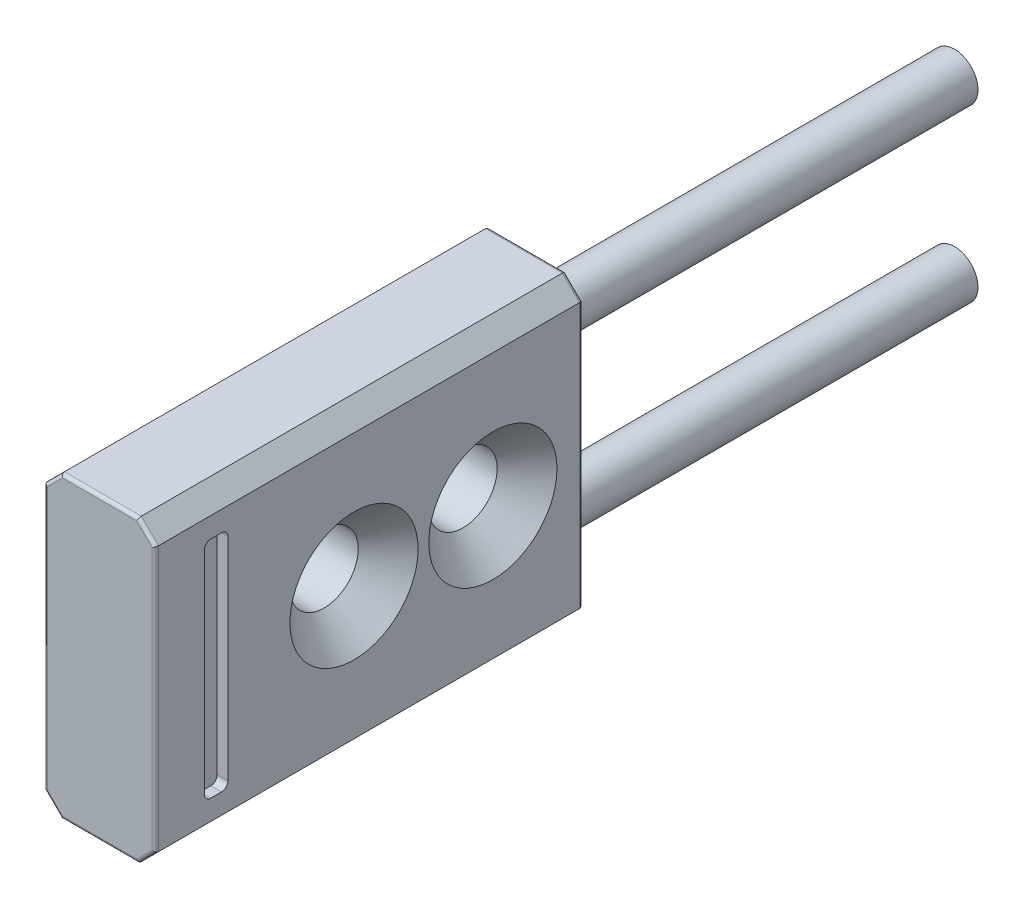
SolidWorks part; units mm, degrees
ref_plane "Front Plane" through (0, 0, 0) normal (0, 0, 1) x (1, 0, 0)
ref_plane "Top Plane" through (0, 0, 0) normal (0, 1, 0) x (1, 0, 0)
ref_plane "Right Plane" through (0, 0, 0) normal (1, 0, 0) x (0, 0, -1)
sketch "Sketch1" plane through (0, 0, 0) normal (1, 0, 0) x (0, 0, -1)
  line L0 (17.1, -7) -> (17.1, 7)
  line L1 (17.1, 7) -> (-2.9, 7)
  line L2 (-2.9, 7) -> (-2.9, -7)
  line L3 (-2.9, -7) -> (17.1, -7)
extrude "Boss-Extrude1" add sketch "Sketch1" against normal blind 5.2
sketch "Sketch2" plane through (0, 0, 0) normal (1, 0, 0) x (0, 0, -1)
  line L0 (0.5, -5.25) -> (0.5, 5.25)
  line L1 (0.5, 5.25) -> (-0.6, 5.25)
  line L2 (-0.6, 5.25) -> (-0.6, -5.25)
  line L3 (-0.6, -5.25) -> (0.5, -5.25)
extrude "Cut-Extrude1" cut sketch "Sketch2" against normal blind 0.5
ref_plane "Plane1" through (0, -4, 0) normal (0, 1, 0) x (1, 0, 0)
sketch "Sketch3" plane through (0, -4, 0) normal (0, 1, 0) x (1, 0, 0)
  line L0 (-1.5, 37.1) -> (-2.6, 37.1)
  line L1 (-2.6, 37.1) -> (-2.6, 17.1)
  line L2 (-2.6, 17.1) -> (-1.5, 17.1)
  line L3 (-1.5, 17.1) -> (-1.5, 37.1)
  line L4 (-2.6, 37.1) -> (-2.6, 17.1) construction
revolve "Revolve1" add sketch "Sketch3" angle 360 about L4
ref_plane "Plane2" through (0, 4, 0) normal (0, 1, 0) x (1, 0, 0)
sketch "Sketch4" plane through (0, 4, 0) normal (0, 1, 0) x (1, 0, 0)
  line L0 (-1.5, 37.1) -> (-2.6, 37.1)
  line L1 (-2.6, 37.1) -> (-2.6, 17.1)
  line L2 (-2.6, 17.1) -> (-1.5, 17.1)
  line L3 (-1.5, 17.1) -> (-1.5, 37.1)
  line L4 (-2.6, 37.1) -> (-2.6, 17.1) construction
revolve "Revolve2" add sketch "Sketch4" angle 360 about L4
hole_wizard "Ø3.2 (3.2) Diameter Hole1" positions "Sketch6" profile "Sketch5" hole size "Ø3.2" standard "ANSI Metric"
sketch "Sketch6" plane through (0, 0, 0) normal (1, 0, 0) x (0, 0, -1)
  point P0 (12.9, 0)
  point P1 (6.4, 0)
sketch "Sketch5" plane through (0, 0, -12.9) normal (0, 1, 0) x (0, 0, -1)
  line L0 (0, 0) -> (0, 5.2)
  line L1 (0, 5.2) -> (1.6, 5.2)
  line L2 (1.6, 5.2) -> (1.6, 0)
  line L5 (1.6, 0) -> (0, 0)
  line L11 (0, -6.35) -> (0, 107.95) construction
  dimension "Thru Hole Dia." = 3.2
  dimension "Thru Hole Depth" = 5.2
chamfer "Chamfer1" distance 0.8 angle 45 4 edges at (0, 7, -7.1) (0, -7, -7.1) (-5.2, -7, -7.1) (-5.2, 7, -7.1)
chamfer "Chamfer2" distance 1.4 angle 45 2 edges at (0, 0, -14.5) (0, 0, -8)
fillet "Fillet1" radius 0.15 16 edges at (-0.4, 6.6, -17.1) (0, 0, -17.1) (-2.6, 7, -17.1) (-0.4, -6.6, -17.1) (-4.8, 6.6, -17.1) (-2.6, -7, -17.1) (-5.2, 0, -17.1) (-4.8, -6.6, -17.1) (-0.4, -6.6, 2.9) (0, 0, 2.9) (-2.6, -7, 2.9) (-0.4, 6.6, 2.9) (-4.8, -6.6, 2.9) (-2.6, 7, 2.9) (-5.2, 0, 2.9) (-4.8, 6.6, 2.9)
fillet "Fillet2" radius 0.3 4 edges at (-0.25, -5.25, 0.6) (-0.25, -5.25, -0.5) (-0.25, 5.25, -0.5) (-0.25, 5.25, 0.6)
